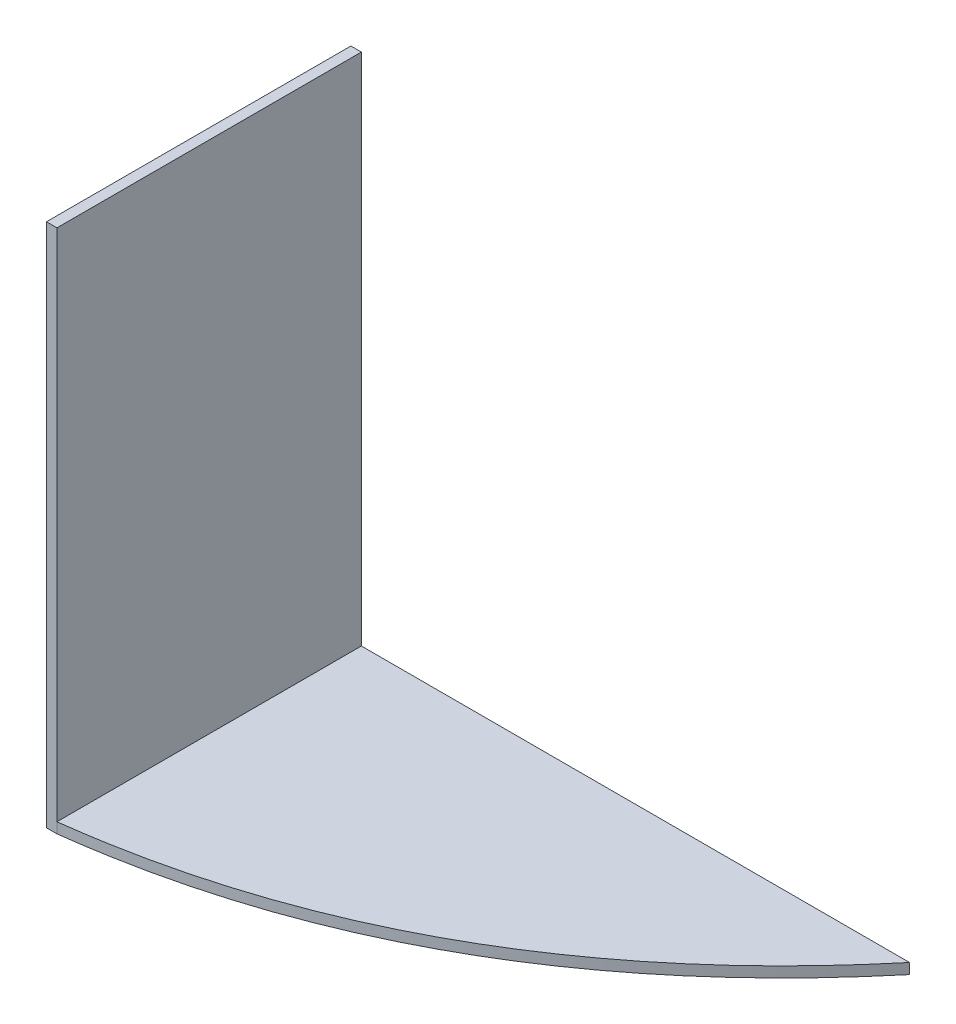
SolidWorks part; units mm, degrees
ref_plane "Front Plane" through (0, 0, 0) normal (0, 0, 1) x (1, 0, 0)
ref_plane "Top Plane" through (0, 0, 0) normal (0, 1, 0) x (1, 0, 0)
ref_plane "Right Plane" through (0, 0, 0) normal (1, 0, 0) x (0, 0, -1)
sketch "Sketch1" plane through (0, 0, 0) normal (0, 0, 1) x (1, 0, 0)
  line L1 (-1.0843, 23.3735) -> (0.9157, 23.3735)
  line L2 (-1.0843, 23.3735) -> (-1.0843, -76.6265)
  line L3 (-1.0843, -76.6265) -> (0.9157, -76.6265)
  line L4 (0.9157, 23.3735) -> (0.9157, -76.6265)
  dimension "D1" = 100
  dimension "D2" = 2
extrude "Boss-Extrude1" add sketch "Sketch1" along normal blind 58
sketch "Sketch2" plane through (0, -76.6265, 0) normal (0, -1, 0) x (1, 0, 0)
  line L0 (0.9157, 58) -> (-1.0843, 58)
  line L1 (-1.0843, 58) -> (-1.0843, 0)
  line L2 (-1.0843, 0) -> (105.3577, 0)
  spline S0 degree 2 poles (0.9157, 58) (63.6174, 50.1879) (105.3577, 0) knots 0 0 0 1 1 1
  point P2 (45.5258, 45.9509)
extrude "Boss-Extrude2" add sketch "Sketch2" against normal blind 2
